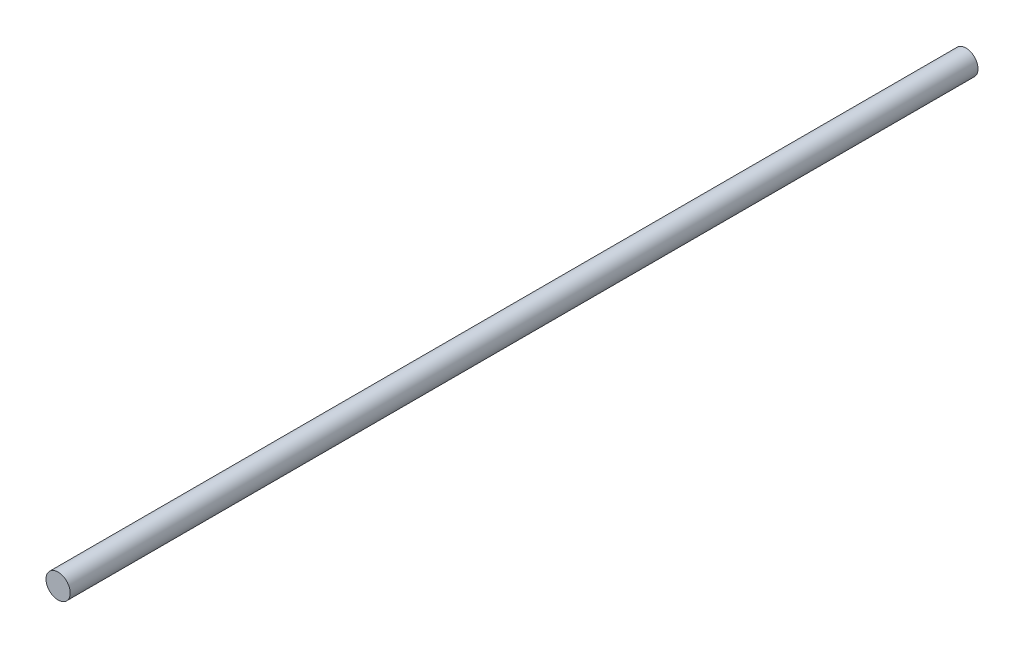
SolidWorks part; units mm, degrees
ref_plane "Plan de face" through (0, 0, 0) normal (0, 0, 1) x (1, 0, 0)
ref_plane "Plan de dessus" through (0, 0, 0) normal (0, 1, 0) x (1, 0, 0)
ref_plane "Plan de droite" through (0, 0, 0) normal (1, 0, 0) x (0, 0, -1)
sketch "Esquisse1" plane through (0, 0, 0) normal (0, 1, 0) x (1, 0, 0)
  line L0 (4, 150) -> (0, 150)
  line L1 (0, 150) -> (0, -150)
  line L2 (0, -150) -> (4, -150)
  line L3 (4, -150) -> (4, 150)
  line L4 (0, 150) -> (0, -150) construction
  dimension "D1" = 300
revolve "Révolution1" add sketch "Esquisse1" angle 360 about L4
